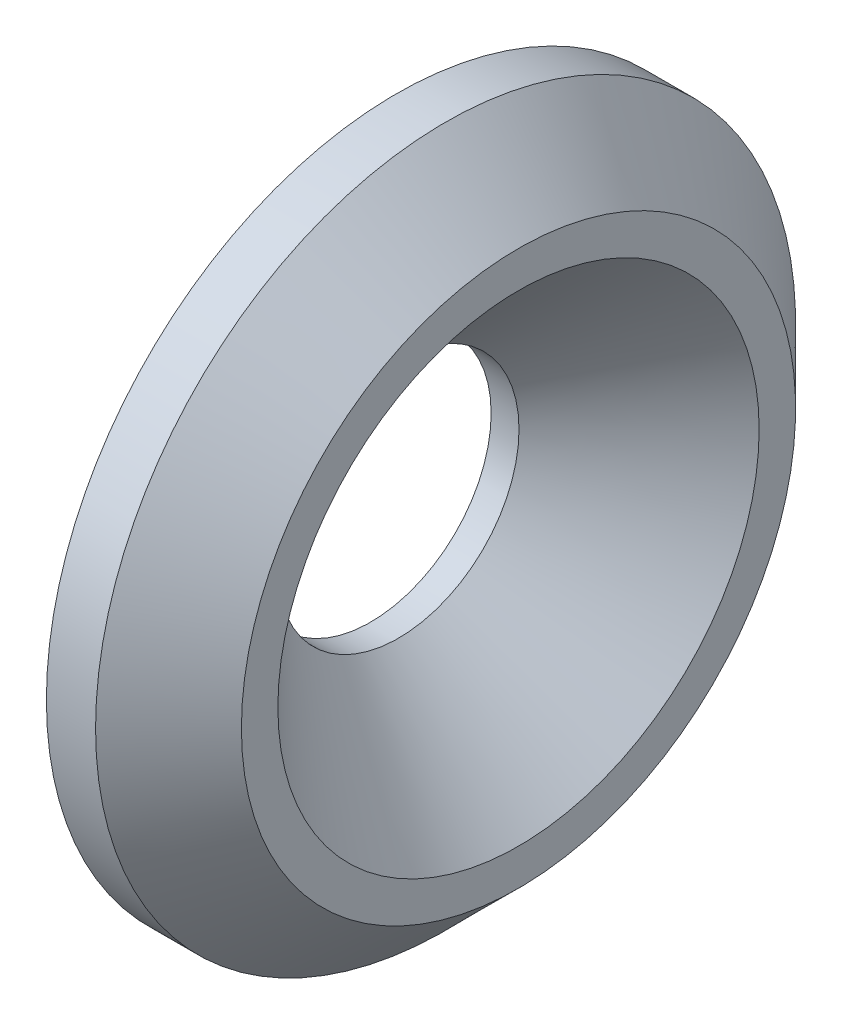
SolidWorks part; units mm, degrees
material "6061-T6 (SS)"
ref_plane "Front" through (0, 0, 0) normal (0, 0, 1) x (1, 0, 0)
ref_plane "Top" through (0, 0, 0) normal (0, 1, 0) x (1, 0, 0)
ref_plane "Right" through (0, 0, 0) normal (1, 0, 0) x (0, 0, -1)
sketch "Sketch1" plane through (0, 0, 0) normal (0, 0, 1) x (1, 0, 0)
  line L0 (443.2878, 232.41) -> (467.7946, 232.41)
  line L1 (467.7946, 232.41) -> (467.7946, 244.475)
  line L2 (467.7946, 244.475) -> (464.6196, 247.65)
  line L3 (464.6196, 247.65) -> (462.4789, 247.65)
  line L4 (462.4789, 247.65) -> (462.4789, 245.11)
  line L5 (462.4789, 245.11) -> (461.3539, 245.11)
  line L6 (461.3539, 245.11) -> (461.3539, 232.41)
  line L7 (461.3539, 220.21) -> (461.3539, 244.61) construction
  line L8 (462.4789, 218.71) -> (462.4789, 245.9853) construction
  dimension "D1" = 45
  dimension "D2" = 15.24
  dimension "D3" = 3.175
  dimension "D4" = 12.7
revolve "Revolve1" add sketch "Sketch1" angle 360 about L0
hole_wizard "Hole1" positions "Sketch2" profile "Sketch4" legacy
sketch "Sketch2" plane through (467.7946, 0, 0) normal (1, 0, 0) x (0, 0, -1)
  circle A0 centre (0, 232.41) radius 12.065 construction
  point P0 (0, 232.41)
sketch "Sketch4" plane through (467.7946, 232.41, 0) normal (0, 1, 0) x (0, 0, -1)
  line L0 (0, 0) -> (0, 19.6645)
  line L1 (0, 19.6645) -> (5.25, 16.51)
  line L2 (5.25, 16.51) -> (5.25, 5.2275)
  line L3 (5.25, 5.2275) -> (10.4775, 0)
  line L5 (10.4775, 0) -> (0, 0)
  line L6 (-5.25, 5.2275) -> (-10.4775, 0) construction
  line L10 (0, 19.6645) -> (-5.25, 16.51) construction
  line L11 (0, -6.35) -> (0, 107.95) construction
  dimension "Hole Dia." = 10.5
  dimension "Hole Depth" = 16.51
  dimension "Near C'Sink Dia." = 20.955
  dimension "Near C'Sink Angle" = 90
  dimension "Drill Angle" = 118
